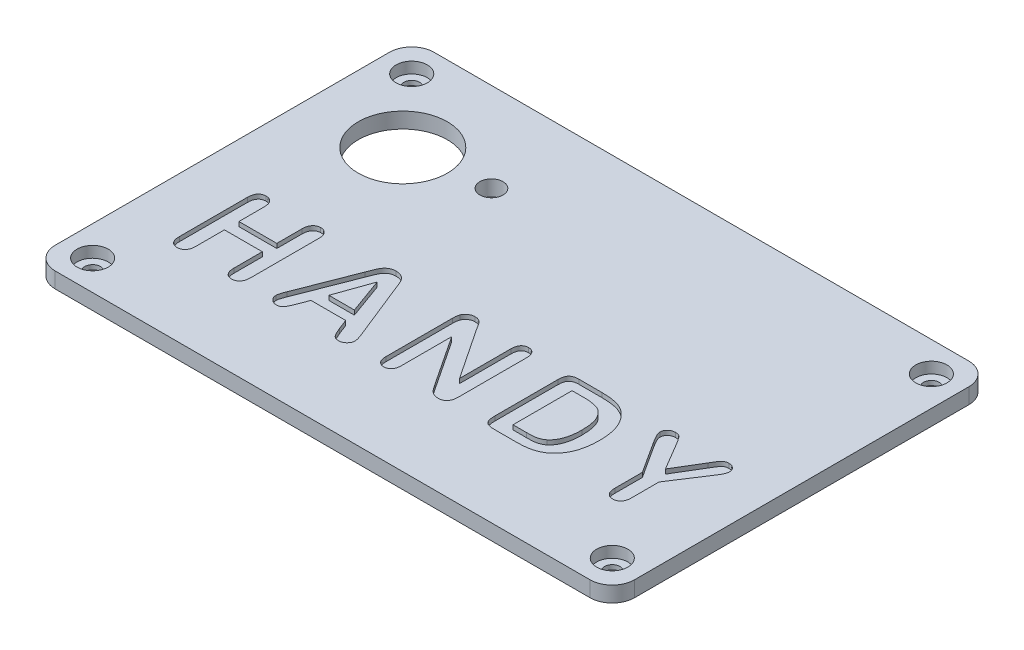
SolidWorks part; units mm, degrees
ref_plane "Piano frontale" through (0, 0, 0) normal (0, 0, 1) x (1, 0, 0)
ref_plane "Piano superiore" through (0, 0, 0) normal (0, 1, 0) x (1, 0, 0)
ref_plane "Piano destro" through (0, 0, 0) normal (1, 0, 0) x (0, 0, -1)
sketch "Schizzo1" plane through (0, 0, 0) normal (0, 1, 0) x (1, 0, 0)
  line L1 (0, 85) -> (130, 85)
  line L2 (0, 85) -> (0, 0)
  line L3 (0, 0) -> (130, 0)
  line L4 (130, 85) -> (130, 0)
  dimension "D1" = 85
  dimension "D2" = 130
extrude "Estrusione-Estrusione1" add sketch "Schizzo1" against normal blind 3.5 contours L1 L4 L3 L2
fillet "Raccordo1" radius 5 1 edges at (130, -1.75, 0)
fillet "Raccordo2" radius 5 1 edges at (130, -1.75, -85)
fillet "Raccordo3" radius 5 1 edges at (0, -1.75, -85)
fillet "Raccordo4" radius 5 1 edges at (0, -1.75, 0)
sketch "Schizzo12" plane through (0, 0, 0) normal (0, 1, 0) x (1, 0, 0)
  line L0 (5, 85) -> (125, 85) construction
  line L1 (0, 80) -> (0, 5) construction
  circle A0 centre (20, 63) radius 10
  dimension "D1" = 20
  dimension "D2" = 22
  dimension "D3" = 20
extrude "Taglio-Estrusione2" cut sketch "Schizzo12" against normal up to surface (3.5 mm away) contours A0 up to face at (65, -3.5, -42.5)
sketch "Schizzo14" plane through (0, 0, 0) normal (0, 1, 0) x (1, 0, 0)
  line L0 (5, 85) -> (125, 85) construction
  circle A0 centre (37.8885, 65) radius 2.6
  circle A1 centre (20, 63) radius 10 construction
  dimension "D1" = 5.2
  dimension "D3" = 18
  dimension "D2" = 20
extrude "Taglio-Estrusione3" cut sketch "Schizzo14" against normal up to surface (3.5 mm away) up to face at (20, -3.5, -53)
sketch "Schizzo28" plane through (0, 0, 0) normal (0, 1, 0) x (1, 0, 0)
  line L0 (0, 18.4779) -> (130, 18.4779) construction
  line L1 (0, 80) -> (0, 5) construction
  line L2 (130, 80) -> (130, 5) construction
  text T0 " HANDY" font "Arial Rounded MT Bold" height 20
extrude "Taglio-Estrusione9" cut sketch "Schizzo28" against normal blind 1
sketch "Schizzo29" plane through (0, 0, 0) normal (0, 1, 0) x (1, 0, 0)
  line L2 (0, 80) -> (0, 5) construction
  line L3 (5, 85) -> (125, 85) construction
  line L4 (5, 0) -> (125, 0) construction
  line L5 (130, 80) -> (130, 5) construction
  circle A0 centre (6.7, 78.3) radius 1.75
  circle A1 centre (6.7, 6.7) radius 1.75
  circle A2 centre (123.3, 6.7) radius 1.75
  circle A3 centre (123.3, 78.3) radius 1.75
  dimension "D3" = 3.5
  dimension "D6" = 3.5
  dimension "D9" = 3.5
  dimension "D12" = 3.5
  dimension "D1" = 6.7
  dimension "D2" = 6.7
  dimension "D4" = 6.7
  dimension "D5" = 6.7
  dimension "D7" = 6.7
  dimension "D8" = 6.7
  dimension "D10" = 6.7
  dimension "D11" = 6.7
extrude "Taglio-Estrusione10" cut sketch "Schizzo29" against normal up to surface (3.5 mm away) up to face at (37.8885, -3.5, -62.4)
sketch "Schizzo30" plane through (0, 0, 0) normal (0, 1, 0) x (1, 0, 0)
  circle A0 centre (6.7, 78.3) radius 3.5
  circle A1 centre (6.7, 6.7) radius 3.5
  circle A2 centre (123.3, 6.7) radius 3.5
  circle A3 centre (123.3, 78.3) radius 3.5
  dimension "D1" = 7
  dimension "D2" = 7
  dimension "D3" = 7
  dimension "D4" = 7
extrude "Taglio-Estrusione11" cut sketch "Schizzo30" against normal blind 2.5
equation "\"2.5mmmm\"=10"
